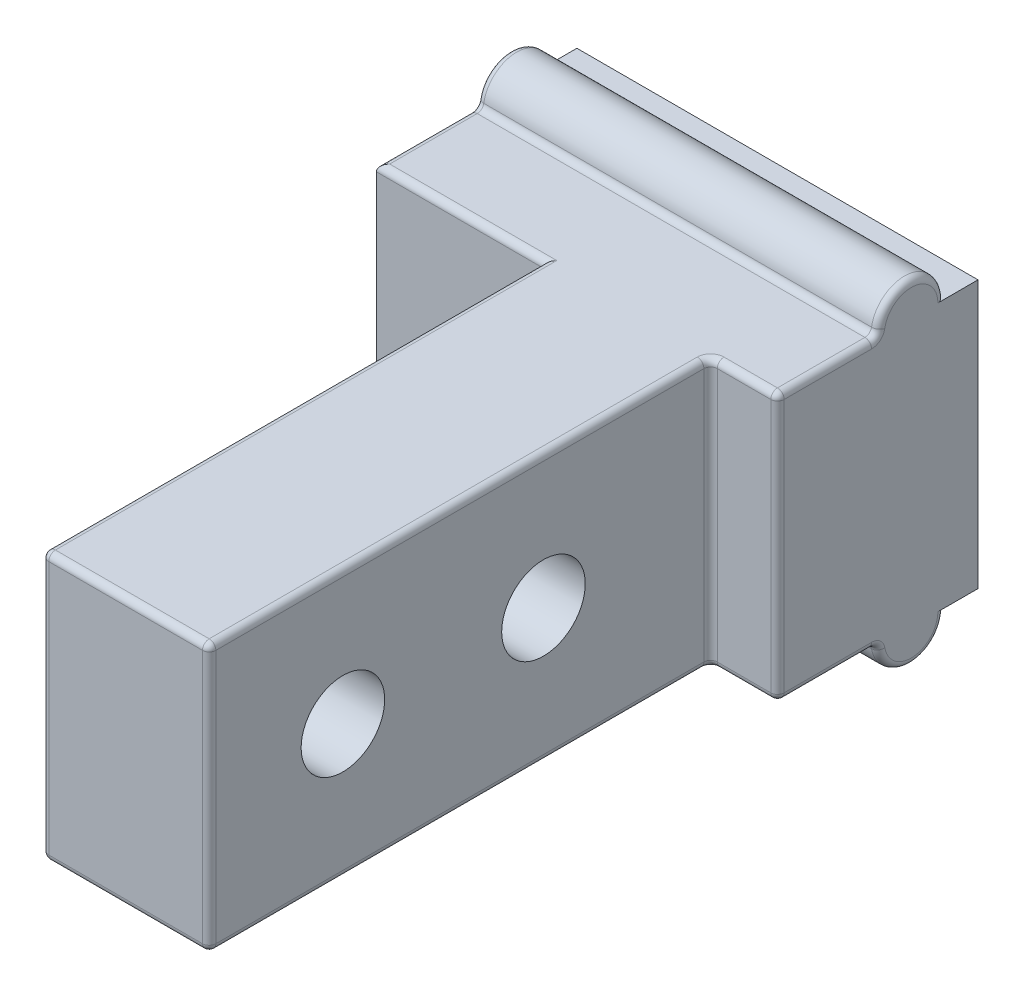
SolidWorks part; units mm, degrees
material "1060-H12"
ref_plane "Front Plane" through (0, 0, 0) normal (0, 0, 1) x (1, 0, 0)
ref_plane "Top Plane" through (0, 0, 0) normal (0, 1, 0) x (1, 0, 0)
ref_plane "Right Plane" through (0, 0, 0) normal (1, 0, 0) x (0, 0, -1)
sketch "Sketch1" plane through (0, 0, 0) normal (1, 0, 0) x (0, 0, -1)
  line L1 (2, -4) -> (-2, -4)
  line L2 (2, -4) -> (2, 4)
  line L3 (2, 4) -> (-2, 4)
  line L4 (-2, -4) -> (-2, 4)
  line L5 (2, -4) -> (-2, 4) construction
  line L6 (2, 4) -> (-2, -4) construction
  circle A0 centre (0, 4) radius 1
  circle A1 centre (0, -4) radius 1
  point P0 (0, 0)
  dimension "D3" = 2
  dimension "D1" = 4
  dimension "D2" = 8
extrude "Boss-Extrude1" add sketch "Sketch1" along normal blind 12 contours A1 L1 L2 L3 A0 L4 | L1 A1
sketch "Sketch2" plane through (0, 0, 2) normal (0, 0, 1) x (1, 0, 0)
  line L4 (0, 4) -> (0, -4)
  line L5 (0, -4) -> (12, -4)
  line L6 (12, -4) -> (12, 4)
  line L7 (12, 4) -> (0, 4)
  line L8 (0, 4) -> (0, -4)
  line L9 (0, -4) -> (12, -4)
  line L10 (12, -4) -> (12, 4)
  line L11 (12, 4) -> (0, 4)
  dimension "D1" = 0
extrude "Boss-Extrude2" add sketch "Sketch2" along normal blind 2
sketch "Sketch3" plane through (0, 0, 4) normal (0, 0, 1) x (1, 0, 0)
  line L0 (12, 4) -> (0, 4) construction
  line L1 (10, -4) -> (5, -4)
  line L2 (10, -4) -> (10, 4)
  line L3 (10, 4) -> (5, 4)
  line L4 (5, -4) -> (5, 4)
  line L5 (10, -4) -> (5, 4) construction
  line L6 (10, 4) -> (5, -4) construction
  line L7 (0, -4) -> (12, -4) construction
  line L9 (0, 4) -> (0, -4) construction
  point P0 (7.5, 0)
  dimension "D1" = 5
  dimension "D2" = 5
extrude "Boss-Extrude3" add sketch "Sketch3" along normal blind 15
sketch "Sketch4" plane through (5, 0, 0) normal (-1, 0, 0) x (0, 0, 1)
  line L0 (4, 0) -> (19, 0) construction
  line L1 (4, 4) -> (4, -4) construction
  line L2 (19, 4) -> (19, -4) construction
  circle A0 centre (15, 0) radius 1.25
  circle A1 centre (9, 0) radius 1.25
  dimension "D1" = 2.5
  dimension "D2" = 6
  dimension "D3" = 4
extrude "Cut-Extrude1" cut sketch "Sketch4" against normal through all both and the other way through all
fillet "Fillet1" radius 0.2 24 edges at (12, -5, 0) (0, -5, 0) (12, 5, 0) (0, 5, 0) (2.5, -4, 4) (5, -4, 11.5) (10, -4, 11.5) (11, -4, 4) (12, -4, 2.5) (6, -4, 1) (0, -4, 2.5) (10, 0, 19) (7.5, -4, 19) (5, 0, 19) (6, 4, 1) (12, 4, 2.5) (11, 4, 4) (10, 4, 11.5) (7.5, 4, 19) (5, 4, 11.5) (2.5, 4, 4) (0, 4, 2.5) (12, 0, 4) (10, 0, 4)
